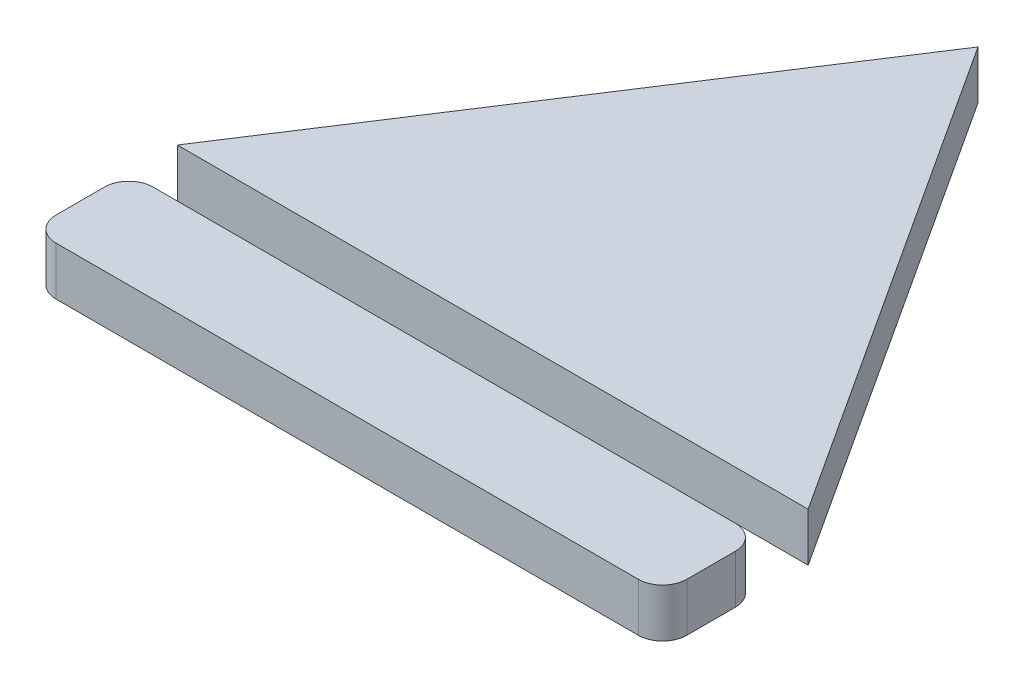
SolidWorks part; units mm, degrees
ref_plane "Front Plane" through (0, 0, 0) normal (0, 0, 1) x (1, 0, 0)
ref_plane "Top Plane" through (0, 0, 0) normal (0, 1, 0) x (1, 0, 0)
ref_plane "Right Plane" through (0, 0, 0) normal (1, 0, 0) x (0, 0, -1)
sketch "Sketch2" plane through (0, 0, 0) normal (0, 1, 0) x (1, 0, 0)
  line L0 (0, 0) -> (13, 0)
  line L1 (13, 0) -> (6.5, 10)
  line L2 (6.5, 10) -> (0, 0)
  line L3 (6.5, 0) -> (6.5, 10) construction
  line L9 (0.5, -1) -> (12.5, -1)
  line L10 (0, -1.5) -> (0, -2.5)
  line L11 (0.5, -3) -> (12.5, -3)
  line L12 (13, -1.5) -> (13, -2.5)
  line L13 (0, -1) -> (13, -3) construction
  line L14 (0, -3) -> (13, -1) construction
  arc A0 (12.5, -3) -> (13, -2.5) centre (12.5, -2.5) ccw
  arc A1 (12.5, -1) -> (13, -1.5) centre (12.5, -1.5) cw
  arc A2 (0.5, -1) -> (0, -1.5) centre (0.5, -1.5) ccw
  arc A3 (0, -2.5) -> (0.5, -3) centre (0.5, -2.5) ccw
  point P5 (6.5, -2)
  point P10 (0, 0)
  dimension "D6" = 0.5
  dimension "D1" = 10
  dimension "D2" = 13
  dimension "D3" = 2
  dimension "D4" = 13
  dimension "D5" = 1
extrude "Boss-Extrude1" add sketch "Sketch2" along normal blind 1
